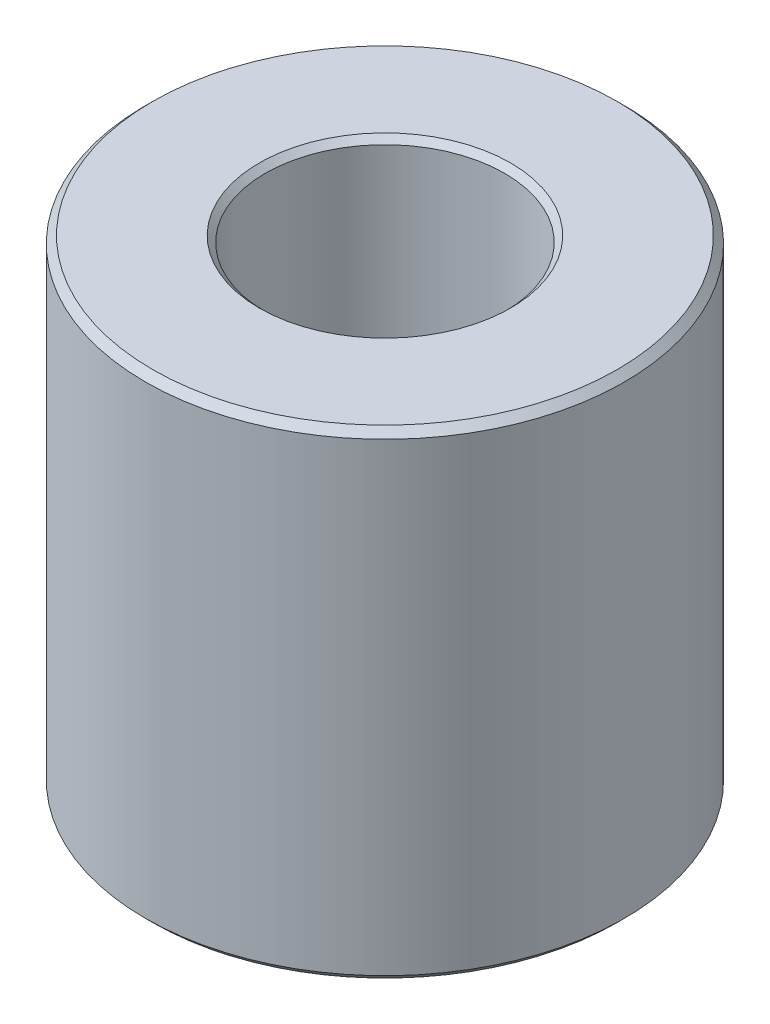
SolidWorks part; units mm, degrees
material "C71500"
ref_plane "Front" through (0, 0, 0) normal (0, 0, 1) x (1, 0, 0)
ref_plane "Top" through (0, 0, 0) normal (0, 1, 0) x (1, 0, 0)
ref_plane "Right" through (0, 0, 0) normal (1, 0, 0) x (0, 0, -1)
sketch "Sketch1" plane through (0, 0, 0) normal (0, 1, 0) x (1, 0, 0)
  circle A0 centre (0, 0) radius 25.4
  dimension "D1" = 50.8
extrude "Extrude1" add sketch "Sketch1" along normal blind 50.8
hole_wizard "1/2 (0.5) Diameter Hole1" positions "Sketch3" profile "Sketch2" hole size "1/2" standard "Ansi Inch" end condition through all
sketch "Sketch3" plane through (0, 50.8, 0) normal (0, 1, 0) x (-1, 0, 0)
  point P0 (0, 0)
sketch "Sketch2" plane through (0, 50.8, 0) normal (1, 0, 0) x (0, 0, 1)
  line L0 (0, 0) -> (0, 50.8)
  line L1 (0, 50.8) -> (6.3627, 50.8)
  line L2 (6.3627, 50.8) -> (6.3627, 0)
  line L5 (6.3627, 0) -> (0, 0)
  line L11 (0, -6.35) -> (0, 107.95) construction
  dimension "Thru Hole Dia." = 12.7254
  dimension "Thru Hole Depth" = 50.8
chamfer "Chamfer1" distance 0.762 angle 45 3 edges at (0, 0, 25.4) (0, 50.8, 25.4) (0, 0, 6.3627)
hole_wizard "1 (1) Diameter Hole1" positions "Sketch5" profile "Sketch4" hole size "1" standard "Ansi Inch"
sketch "Sketch5" plane through (0, 50.8, 0) normal (0, 1, 0) x (-1, 0, 0)
  point P0 (0, 0)
sketch "Sketch4" plane through (0, 50.8, 0) normal (1, 0, 0) x (0, 0, 1)
  line L0 (0, 0) -> (0, 42.418)
  line L1 (0, 42.418) -> (12.7, 42.418)
  line L2 (12.7, 42.418) -> (12.7, 0)
  line L5 (12.7, 0) -> (0, 0)
  line L10 (0, 42.418) -> (-12.7, 42.418) construction
  line L11 (0, -6.35) -> (0, 107.95) construction
  dimension "Hole Dia." = 25.4
  dimension "Hole Depth" = 42.418
  dimension "Drill Angle" = 180
chamfer "Chamfer2" distance 0.254 angle 45 1 edges at (0, 8.382, 12.7)
chamfer "Chamfer3" distance 0.635 angle 45 1 edges at (0, 50.8, 12.7)
